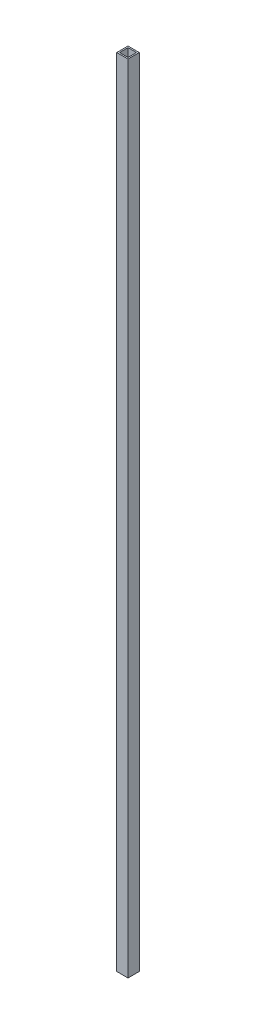
SolidWorks part; units mm, degrees
ref_plane "Piano frontale" through (0, 0, 0) normal (0, 0, 1) x (1, 0, 0)
ref_plane "Piano superiore" through (0, 0, 0) normal (0, 1, 0) x (1, 0, 0)
ref_plane "Piano destro" through (0, 0, 0) normal (1, 0, 0) x (0, 0, -1)
sketch "Schizzo1" plane through (0, 0, 0) normal (0, 1, 0) x (1, 0, 0)
  line L0 (15, 15) -> (-15, 15)
  line L1 (20, -20) -> (-20, -20)
  line L2 (20, -20) -> (20, 20)
  line L3 (20, 20) -> (-20, 20)
  line L4 (-20, -20) -> (-20, 20)
  line L5 (20, -20) -> (-20, 20) construction
  line L6 (20, 20) -> (-20, -20) construction
  line L7 (-15, -15) -> (-15, 15)
  line L8 (15, -15) -> (-15, -15)
  line L9 (15, -15) -> (15, 15)
  point P0 (0, 0)
  dimension "D1" = 40
  dimension "D2" = 40
  dimension "D3" = 5
extrude "Estrusione-Estrusione1" add sketch "Schizzo1" along normal mid plane 2817
